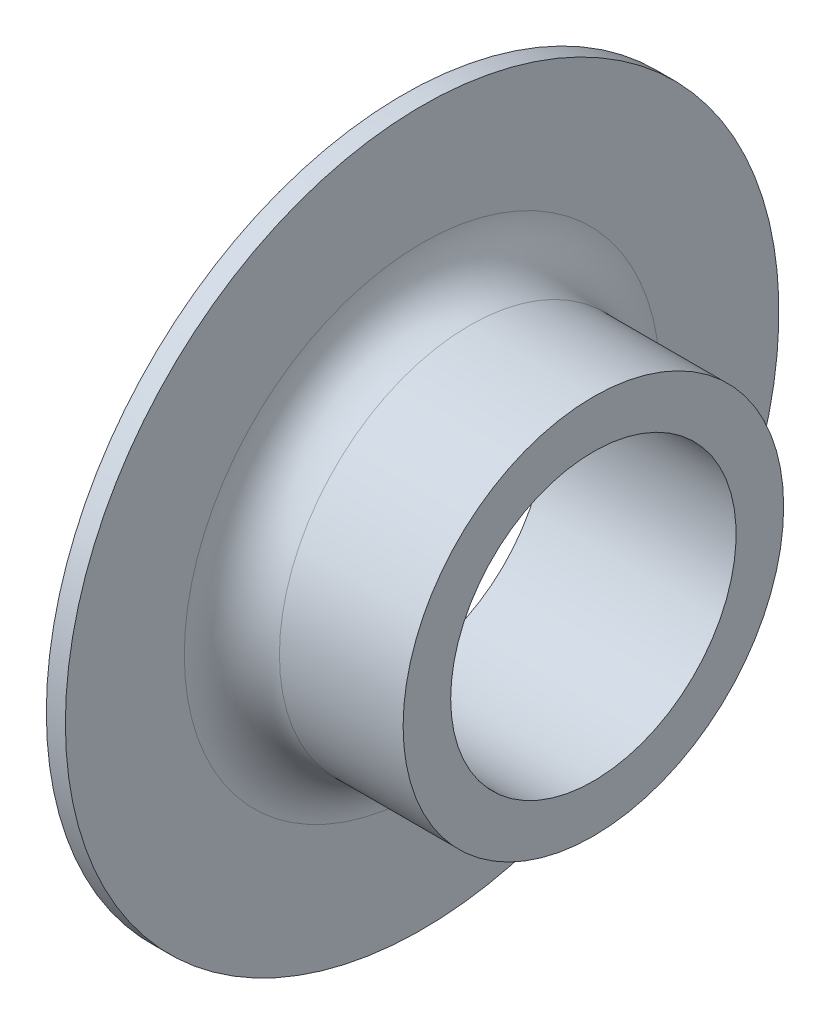
SolidWorks part; units mm, degrees
ref_plane "Front Plane" through (0, 0, 0) normal (0, 0, 1) x (1, 0, 0)
ref_plane "Top Plane" through (0, 0, 0) normal (0, 1, 0) x (1, 0, 0)
ref_plane "Right Plane" through (0, 0, 0) normal (1, 0, 0) x (0, 0, -1)
sketch "Çizim1" plane through (0, 0, 0) normal (0, 0, 1) x (1, 0, 0)
  line L6 (0, 37.5) -> (0, -37.5) construction
  line L7 (0, 37.5) -> (2, 37.5)
  line L8 (2, 37.5) -> (2, 20)
  line L9 (2, 20) -> (20, 20)
  line L10 (20, 20) -> (20, 15)
  line L11 (20, 15) -> (0, 15)
  line L12 (0, 15) -> (0, 37.5)
  line L13 (0, 0) -> (18, 0) construction
  point P4 (0, 0)
  dimension "D1" = 75
  dimension "D2" = 2
  dimension "D3" = 5
  dimension "D4" = 20
  dimension "D5" = 15
revolve "Döndür1" add sketch "Çizim1" angle 360 about L13
fillet "Radyus1" radius 5 1 edges at (2, 0, 20)
